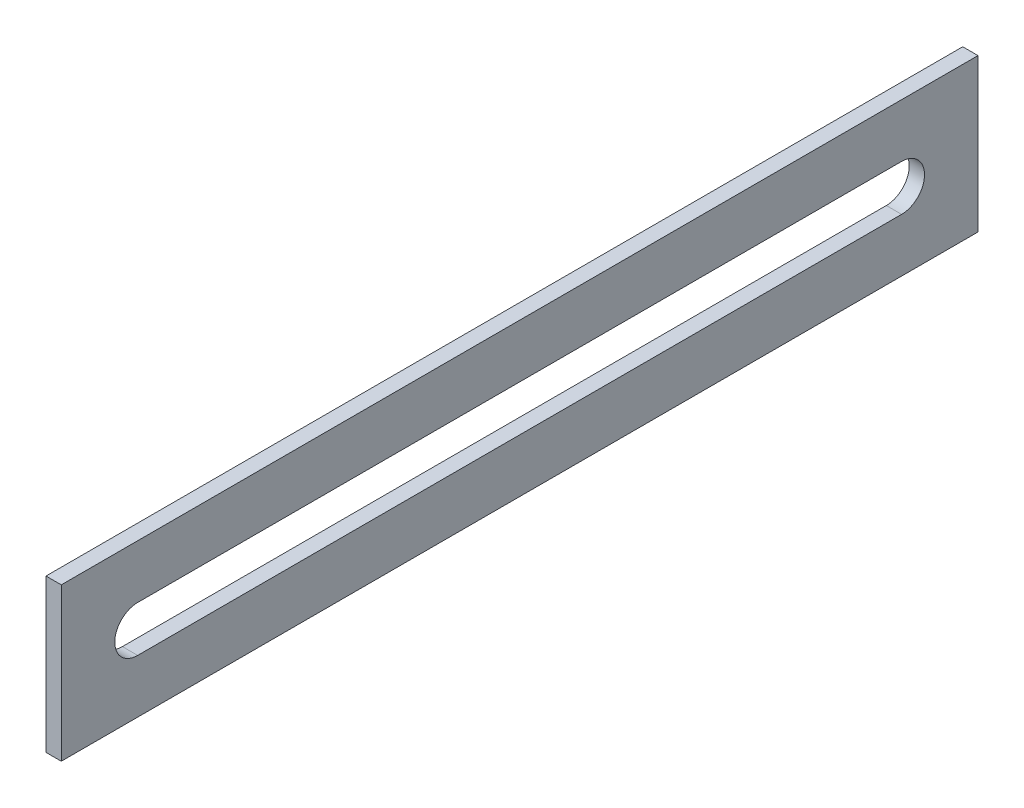
SolidWorks part; units mm, degrees
ref_plane "前视基准面" through (0, 0, 0) normal (0, 0, 1) x (1, 0, 0)
ref_plane "上视基准面" through (0, 0, 0) normal (0, 1, 0) x (1, 0, 0)
ref_plane "右视基准面" through (0, 0, 0) normal (1, 0, 0) x (0, 0, -1)
sketch "草图1" plane through (0, 0, 0) normal (1, 0, 0) x (0, 0, -1)
  line L0 (3.434, 6.122) -> (53.434, 6.122)
  line L1 (-1.566, 9.622) -> (58.434, 9.622)
  line L2 (-1.566, 9.622) -> (-1.566, -0.378)
  line L3 (-1.566, -0.378) -> (58.434, -0.378)
  line L4 (58.434, 9.622) -> (58.434, -0.378)
  line L6 (3.434, 3.122) -> (53.434, 3.122)
  arc A0 (3.434, 3.122) -> (3.434, 6.122) centre (3.434, 4.622) cw
  arc A1 (53.434, 6.122) -> (53.434, 3.122) centre (53.434, 4.622) cw
  dimension "D1" = 10
  dimension "D2" = 60
  dimension "D3" = 3
  dimension "D4" = 3.5
  dimension "D5" = 50
  dimension "D6" = 5
  dimension "D7" = 50
  dimension "D8" = 5
extrude "凸台-拉伸1" add sketch "草图1" along normal blind 1
